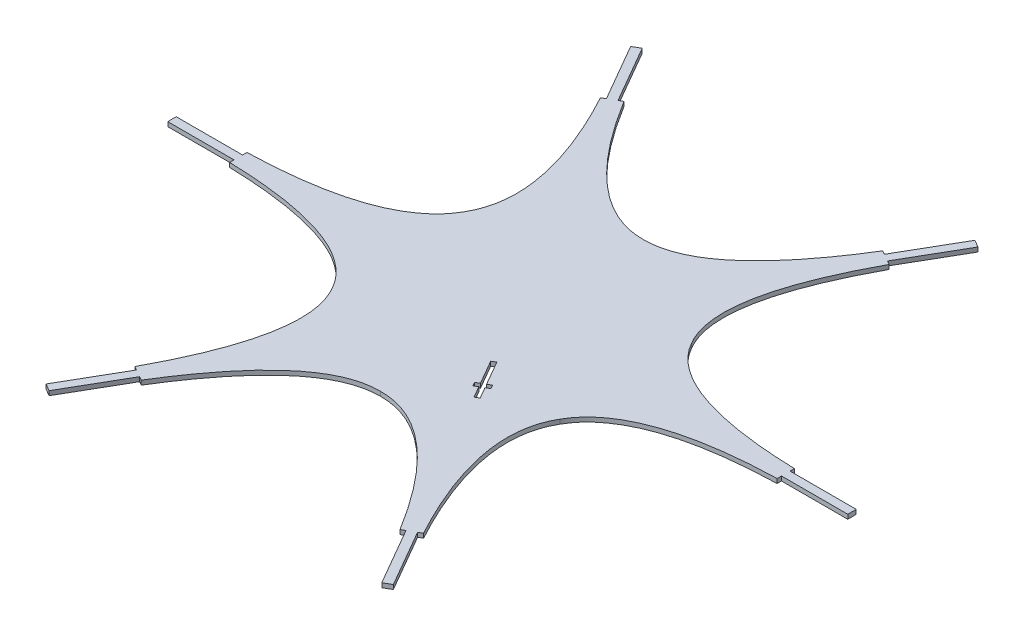
SolidWorks part; units mm, degrees
ref_plane "Front Plane" through (0, 0, 0) normal (0, 0, 1) x (1, 0, 0)
ref_plane "Top Plane" through (0, 0, 0) normal (0, 1, 0) x (1, 0, 0)
ref_plane "Right Plane" through (0, 0, 0) normal (1, 0, 0) x (0, 0, -1)
sketch "Sketch1" plane through (0, -95.6486, 0) normal (0, -1, 0) x (-1, 0, 0)
  line L0 (-274.8977, -1.3497) -> (-274.8977, -17.0997) construction
  line L1 (-214.4278, -259.2247) -> (285.5722, -259.2247) construction
  line L2 (-214.4278, -259.2247) -> (-214.4278, 240.7753) construction
  line L3 (-214.4278, 240.7753) -> (285.5722, 240.7753) construction
  line L4 (285.5722, -259.2247) -> (285.5722, 240.7753) construction
  line L5 (-214.4278, -259.2247) -> (285.5722, 240.7753) construction
  line L6 (-214.4278, 240.7753) -> (285.5722, -259.2247) construction
  line L7 (-242.8231, -1.3497) -> (-274.8977, -1.3497) construction
  line L8 (-274.8977, -17.0997) -> (-242.8231, -17.0997) construction
  line L9 (35.5722, -9.2247) -> (-306.2138, -9.2247) construction
  line L10 (-112.8428, 263.5877) -> (-126.4827, 255.7127) construction
  line L11 (-119.6627, 259.6502) -> (-274.8977, -9.2247) construction
  line L12 (35.5722, -9.2247) -> (-197.2802, 125.2128) construction
  line L13 (-123.0186, 257.7127) -> (-116.3069, 261.5877)
  line L14 (-116.3069, 261.5877) -> (-100.2696, 233.8103) construction
  line L15 (-106.9813, 229.9353) -> (-123.0186, 257.7127) construction
  line L16 (-116.3069, 261.5877) -> (-86.0569, 209.1932)
  line L17 (-97.4781, 228.9752) -> (-73.6484, 187.7011) construction
  line L18 (-86.0569, 209.1932) -> (-82.5928, 211.1932)
  line L19 (-70.1843, 189.7011) -> (-94.014, 230.9752) construction
  line L20 (-119.6627, 259.6502) -> (-87.1117, 203.2702) construction
  line L21 (-92.7686, 205.3182) -> (-96.2327, 203.3182)
  line L22 (-123.0186, 257.7127) -> (-92.7686, 205.3182)
  line L23 (-68.3508, 50.7753) -> (-137.2775, -68.6092) construction
  line L24 (157.2014, 209.1932) -> (153.7373, 211.1932)
  line L25 (187.4514, 261.5877) -> (157.2014, 209.1932)
  line L26 (163.9131, 205.3182) -> (167.3772, 203.3182)
  line L27 (194.1631, 257.7127) -> (163.9131, 205.3182)
  line L28 (187.4514, 261.5877) -> (194.1631, 257.7127)
  line L29 (285.5422, -5.3497) -> (285.5422, -1.3497)
  line L30 (346.0422, -5.3497) -> (285.5422, -5.3497)
  line L31 (285.5422, -13.0997) -> (285.5422, -17.0997)
  line L32 (346.0422, -13.0997) -> (285.5422, -13.0997)
  line L33 (346.0422, -5.3497) -> (346.0422, -13.0997)
  line L34 (163.9131, -223.7675) -> (167.3772, -221.7675)
  line L35 (194.1631, -276.162) -> (163.9131, -223.7675)
  line L36 (157.2014, -227.6425) -> (153.7373, -229.6425)
  line L37 (187.4514, -280.037) -> (157.2014, -227.6425)
  line L38 (194.1631, -276.162) -> (187.4514, -280.037)
  line L39 (-86.0569, -227.6425) -> (-82.5928, -229.6425)
  line L40 (-116.3069, -280.037) -> (-86.0569, -227.6425)
  line L41 (-92.7686, -223.7675) -> (-96.2327, -221.7675)
  line L42 (-123.0186, -276.162) -> (-92.7686, -223.7675)
  line L43 (-116.3069, -280.037) -> (-123.0186, -276.162)
  line L44 (-214.3977, -13.0997) -> (-214.3977, -17.0997)
  line L45 (-274.8977, -13.0997) -> (-214.3977, -13.0997)
  line L46 (-214.3977, -5.3497) -> (-214.3977, -1.3497)
  line L47 (-274.8977, -5.3497) -> (-214.3977, -5.3497)
  line L48 (-274.8977, -13.0997) -> (-274.8977, -5.3497)
  line L49 (5.6168, -53.1091) -> (9.0809, -55.1091) construction
  line L50 (9.0809, -55.1091) -> (-11.6753, -91.0598) construction
  line L52 (-11.6753, -91.0598) -> (-15.1394, -89.0598) construction
  line L54 (-15.1394, -89.0598) -> (5.6168, -53.1091) construction
  line L55 (9.1492, -55.0908) -> (-3.657, -77.2717)
  line L56 (-11.657, -91.1281) -> (-15.2077, -89.0781)
  line L57 (-15.2077, -89.0781) -> (-9.2077, -78.6858)
  line L58 (5.5985, -53.0408) -> (9.1492, -55.0908)
  line L59 (-7.2077, -75.2217) -> (-3.657, -77.2717) construction
  line L60 (-7.2077, -75.2217) -> (-10.6718, -73.2217) construction
  line L61 (-3.657, -77.2717) -> (-0.1929, -79.2717) construction
  line L62 (-10.6718, -73.2217) -> (-12.6718, -76.6858)
  line L63 (-12.6718, -76.6858) -> (-9.2077, -78.6858)
  line L64 (-2.1929, -82.7358) -> (-0.1929, -79.2717)
  line L65 (-0.1929, -79.2717) -> (-3.657, -77.2717)
  line L66 (-7.2077, -75.2217) -> (5.5985, -53.0408)
  line L67 (-5.657, -80.7358) -> (-11.657, -91.1281)
  line L68 (-15.2077, -89.0781) -> (5.5985, -53.0408) construction
  line L69 (-10.6718, -73.2217) -> (-7.2077, -75.2217)
  line L70 (9.1492, -55.0908) -> (-11.657, -91.1281) construction
  line L71 (-5.657, -80.7358) -> (-2.1929, -82.7358)
  circle A0 centre (35.5722, -9.2247) radius 250 construction
  spline S0 degree 2 poles (-96.2327, 203.3182) (-39.7989, 98.9516) (-68.3508, 50.7753) knots 0 0 0 1 1 1
  spline S1 degree 2 poles (-214.3977, -1.3497) (-95.7967, 1.9606) (-68.3508, 50.7753) knots 0 0 0 1 1 1
  spline S2 degree 2 poles (153.7373, 211.1932) (91.5701, 110.1368) (35.5722, 110.7753) knots 0 0 0 1 1 1
  spline S3 degree 2 poles (-82.5928, 211.1932) (-20.4256, 110.1368) (35.5722, 110.7753) knots 0 0 0 1 1 1
  spline S4 degree 2 poles (285.5422, -1.3497) (166.9412, 1.9606) (139.4953, 50.7753) knots 0 0 0 1 1 1
  spline S5 degree 2 poles (167.3772, 203.3182) (110.9434, 98.9516) (139.4953, 50.7753) knots 0 0 0 1 1 1
  spline S6 degree 2 poles (167.3772, -221.7675) (110.9434, -117.4009) (139.4953, -69.2247) knots 0 0 0 1 1 1
  spline S7 degree 2 poles (285.5422, -17.0997) (166.9412, -20.4099) (139.4953, -69.2247) knots 0 0 0 1 1 1
  spline S8 degree 2 poles (-82.5928, -229.6425) (-20.4256, -128.5861) (35.5722, -129.2247) knots 0 0 0 1 1 1
  spline S9 degree 2 poles (153.7373, -229.6425) (91.5701, -128.5861) (35.5722, -129.2247) knots 0 0 0 1 1 1
  spline S10 degree 2 poles (-214.3977, -17.0997) (-95.7967, -20.4099) (-68.3508, -69.2247) knots 0 0 0 1 1 1
  spline S11 degree 2 poles (-96.2327, -221.7675) (-39.7989, -117.4009) (-68.3508, -69.2247) knots 0 0 0 1 1 1
  point P0 (35.5722, -9.2247)
  point P74 (0, 0)
  point P83 (35.5722, -9.2247)
  point P97 (0, 0)
  dimension "Diam Base Estática" = 500
  dimension "D1" = 120
  dimension "D3" = 120
  dimension "D4" = 120
  dimension "D5" = 120
  dimension "D6" = 120
  dimension "D7" = 120
  dimension "D9" = 16
  dimension "D10" = 4
  dimension "D11" = 4
  dimension "D12" = 4
  dimension "D8" = 0.05
  dimension "D2" = 6
extrude "Boss-Extrude1" add sketch "Sketch1" along normal blind 4
equation "\"D3@Sketch1\"=\"D1@Sketch1\""
equation "\"D4@Sketch1\"=\"D1@Sketch1\""
equation "\"D5@Sketch1\"=\"D1@Sketch1\""
equation "\"D6@Sketch1\"=\"D1@Sketch1\""
equation "\"D7@Sketch1\"=\"D1@Sketch1\""
equation "\"D12@Sketch1\"=\"D11@Sketch1\""
